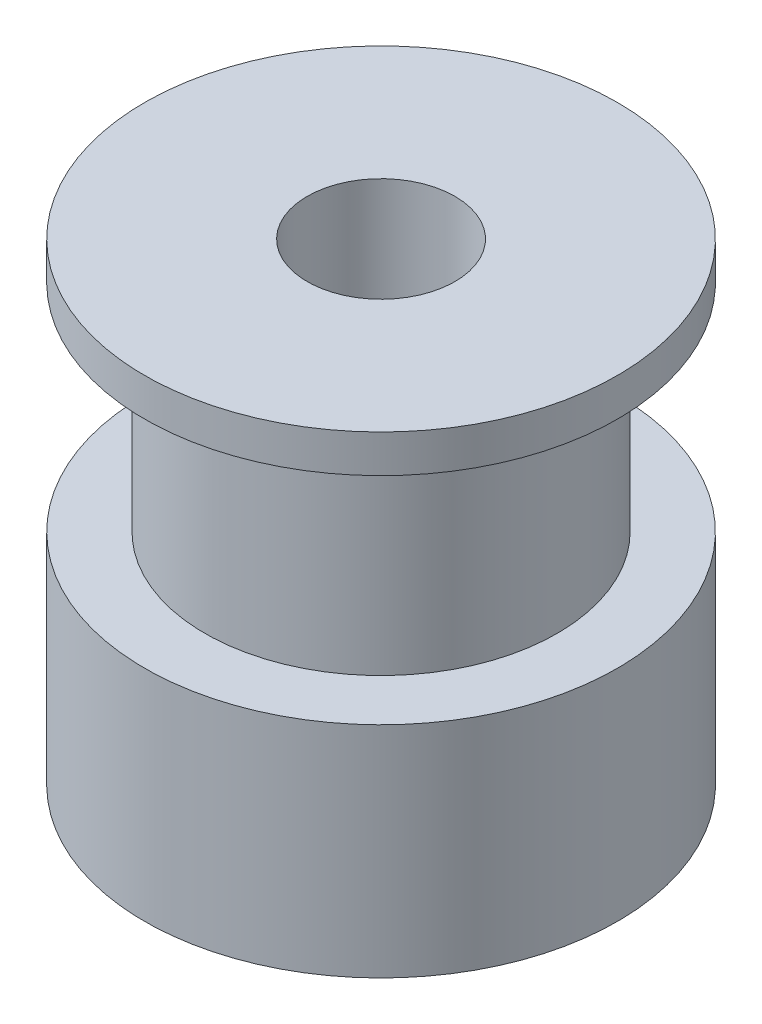
SolidWorks part; units mm, degrees
ref_plane "Front Plane" through (0, 0, 0) normal (0, 0, 1) x (1, 0, 0)
ref_plane "Top Plane" through (0, 0, 0) normal (0, 1, 0) x (1, 0, 0)
ref_plane "Right Plane" through (0, 0, 0) normal (1, 0, 0) x (0, 0, -1)
sketch "Sketch1" plane through (0, 0, 0) normal (0, 0, 1) x (1, 0, 0)
  line L0 (2.5, 0) -> (2.5, 16)
  line L1 (2.5, 16) -> (8, 16)
  line L2 (8, 16) -> (8, 14.72)
  line L3 (8, 14.72) -> (5.96, 14.72)
  line L4 (5.96, 14.72) -> (5.96, 7.42)
  line L5 (5.96, 7.42) -> (8, 7.42)
  line L6 (8, 7.42) -> (8, 0)
  line L7 (8, 0) -> (2.5, 0)
  line L8 (0, 0) -> (0, 16) construction
  line L9 (5.96, 12.1233) -> (0, 12.1233) construction
  dimension "D1" = 5
  dimension "D2" = 16
  dimension "D3" = 11.92
  dimension "D4" = 16
  dimension "D5" = 7.42
  dimension "D6" = 7.3
revolve "Revolve1" add sketch "Sketch1" angle 360 about L8
ref_plane "Plane1" through (0, 12.1233, 0) normal (0, 1, 0) x (1, 0, 0)
